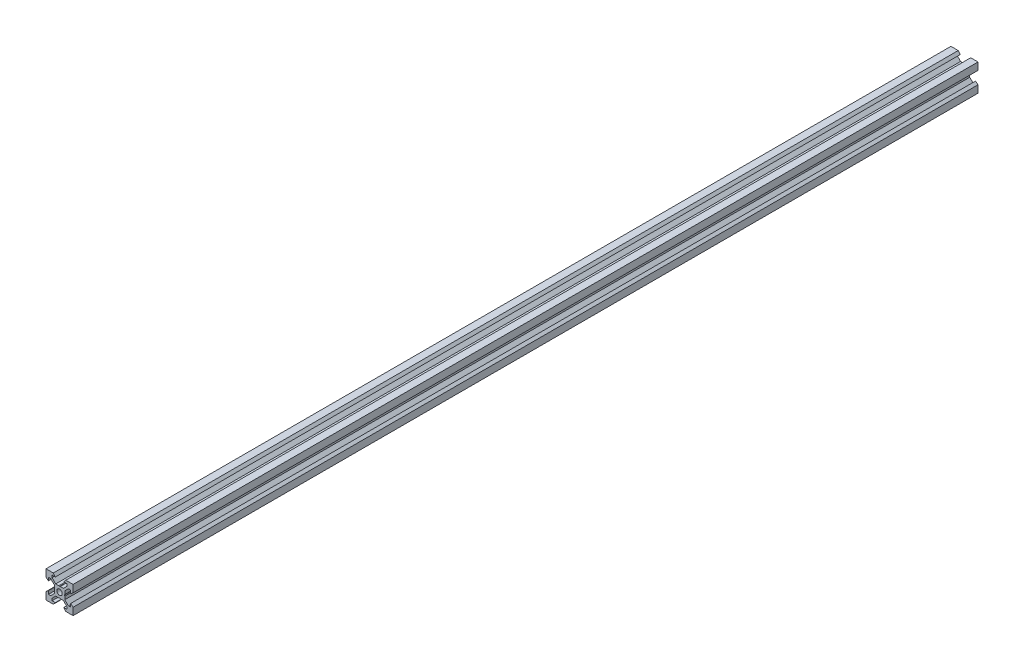
SolidWorks part; units mm, degrees
ref_plane "Front Plane" through (0, 0, 0) normal (0, 0, 1) x (1, 0, 0)
ref_plane "Top Plane" through (0, 0, 0) normal (0, 1, 0) x (1, 0, 0)
ref_plane "Right Plane" through (0, 0, 0) normal (1, 0, 0) x (0, 0, -1)
sketch "Sketch1" plane through (0, 0, 0) normal (0, 0, 1) x (1, 0, 0)
  line L0 (10, 10) -> (4.6104, 10) construction
  line L1 (10, 10) -> (10, 4.6104) construction
  line L2 (10, -10) -> (10, -4.6104) construction
  line L3 (10, -10) -> (4.6104, -10) construction
  line L4 (10, 10) -> (10, 4.6104)
  line L5 (6.5607, 5.5) -> (8.2, 5.5)
  line L6 (5.5, 8.2) -> (5.5, 6.5607)
  line L7 (10, 10) -> (4.6104, 10)
  line L8 (10, 10) -> (10, 4.6104)
  line L9 (6.5607, 5.5) -> (3.9, 2.8393)
  line L10 (5.5, 6.5607) -> (2.8393, 3.9)
  line L11 (10, 4.6104) -> (8.2, 3.1)
  line L12 (4.6104, 10) -> (3.1, 8.2)
  line L13 (8.2, 3.1) -> (8.2, 5.5)
  line L14 (3.1, 8.2) -> (5.5, 8.2)
  line L15 (-6.5607, 5.5) -> (-8.2, 5.5)
  line L16 (6.5607, -5.5) -> (8.2, -5.5)
  line L17 (3.1, -8.2) -> (5.5, -8.2)
  line L18 (8.2, -3.1) -> (8.2, -5.5)
  line L19 (4.6104, -10) -> (3.1, -8.2)
  line L20 (10, -4.6104) -> (8.2, -3.1)
  line L21 (0.5196, -3.9) -> (0, -3.6)
  line L22 (0.5196, 3.9) -> (0, 3.6)
  line L23 (3.6, 0) -> (3.9, -0.5196)
  line L24 (3.9, 0.5196) -> (3.6, 0)
  line L25 (3.9, 0.5196) -> (3.9, 2.8393)
  line L26 (2.8393, 3.9) -> (0.5196, 3.9)
  line L27 (3.9, -2.8393) -> (3.9, -0.5196)
  line L28 (2.8393, -3.9) -> (0.5196, -3.9)
  line L29 (5.5, -6.5607) -> (2.8393, -3.9)
  line L30 (6.5607, -5.5) -> (3.9, -2.8393)
  line L31 (10, -10) -> (10, -4.6104)
  line L32 (10, -10) -> (4.6104, -10)
  line L33 (5.5, -8.2) -> (5.5, -6.5607)
  line L34 (-6.5607, -5.5) -> (-8.2, -5.5)
  line L35 (10, -10) -> (10, -4.6104)
  line L36 (0, 0) -> (0, 8.2) construction
  line L37 (-10, -10) -> (-4.6104, -10) construction
  line L38 (-10, -10) -> (-10, -4.6104) construction
  line L39 (-10, 10) -> (-10, 4.6104) construction
  line L40 (-10, 10) -> (-4.6104, 10) construction
  line L41 (-10, -10) -> (-10, -4.6104)
  line L43 (-5.5, -8.2) -> (-5.5, -6.5607)
  line L44 (-10, -10) -> (-4.6104, -10)
  line L45 (-10, -10) -> (-10, -4.6104)
  line L46 (-6.5607, -5.5) -> (-3.9, -2.8393)
  line L47 (-5.5, -6.5607) -> (-2.8393, -3.9)
  line L48 (-2.8393, -3.9) -> (-0.5196, -3.9)
  line L49 (-3.9, -2.8393) -> (-3.9, -0.5196)
  line L50 (-2.8393, 3.9) -> (-0.5196, 3.9)
  line L51 (-3.9, 0.5196) -> (-3.9, 2.8393)
  line L52 (-3.9, 0.5196) -> (-3.6, 0)
  line L53 (-3.6, 0) -> (-3.9, -0.5196)
  line L54 (-0.5196, 3.9) -> (0, 3.6)
  line L55 (-0.5196, -3.9) -> (0, -3.6)
  line L56 (-10, -4.6104) -> (-8.2, -3.1)
  line L57 (-4.6104, -10) -> (-3.1, -8.2)
  line L58 (-8.2, -3.1) -> (-8.2, -5.5)
  line L59 (-3.1, -8.2) -> (-5.5, -8.2)
  line L60 (-10, -10) -> (10, -10) construction
  line L61 (-10, -10) -> (-10, 10) construction
  line L62 (-3.1, 8.2) -> (-5.5, 8.2)
  line L63 (-8.2, 3.1) -> (-8.2, 5.5)
  line L64 (-4.6104, 10) -> (-3.1, 8.2)
  line L65 (-10, 4.6104) -> (-8.2, 3.1)
  line L66 (-5.5, 6.5607) -> (-2.8393, 3.9)
  line L67 (-6.5607, 5.5) -> (-3.9, 2.8393)
  line L68 (-10, 10) -> (-10, 4.6104)
  line L69 (-10, 10) -> (-4.6104, 10)
  line L70 (-5.5, 8.2) -> (-5.5, 6.5607)
  line L71 (-10, 10) -> (10, 10) construction
  line L72 (-10, 10) -> (-10, 4.6104)
  line L73 (10, -10) -> (10, 10) construction
  line L74 (-10, -10) -> (10, 10) construction
  line L75 (-10, 10) -> (10, -10) construction
  circle A0 centre (0, 0) radius 2
  dimension "D7" = 4
  dimension "D1" = 20
  dimension "D2" = 5.3896
  dimension "D3" = 4.5
  dimension "D4" = 50
  dimension "D5" = 1.8
  dimension "D6" = 1.5104
  dimension "D8" = 5.5
  dimension "D9" = 120
  dimension "D10" = 0.3
  dimension "D11" = 2.3197
  dimension "D12" = 7.8
  dimension "D13" = 7.8
  dimension "D14" = 1.5
  dimension "D15" = 2.6607
extrude "Boss-Extrude1" add sketch "Sketch1" along normal mid plane 668.38 contours L70 L62 L64 L69 L68 L65 L63 L15 L67 L51 L52 L53 L49 L46 L34 L58 L56 L41 L44 L57 L59 L43 L47 L48 L55 L21 L28 L29 L33 L17 L19 L32 L31 L20 L18 L16 L30 L27 L23 L24 L25 L9 L5 L13 L11 L4 L7 L12 L14 L6 L10
